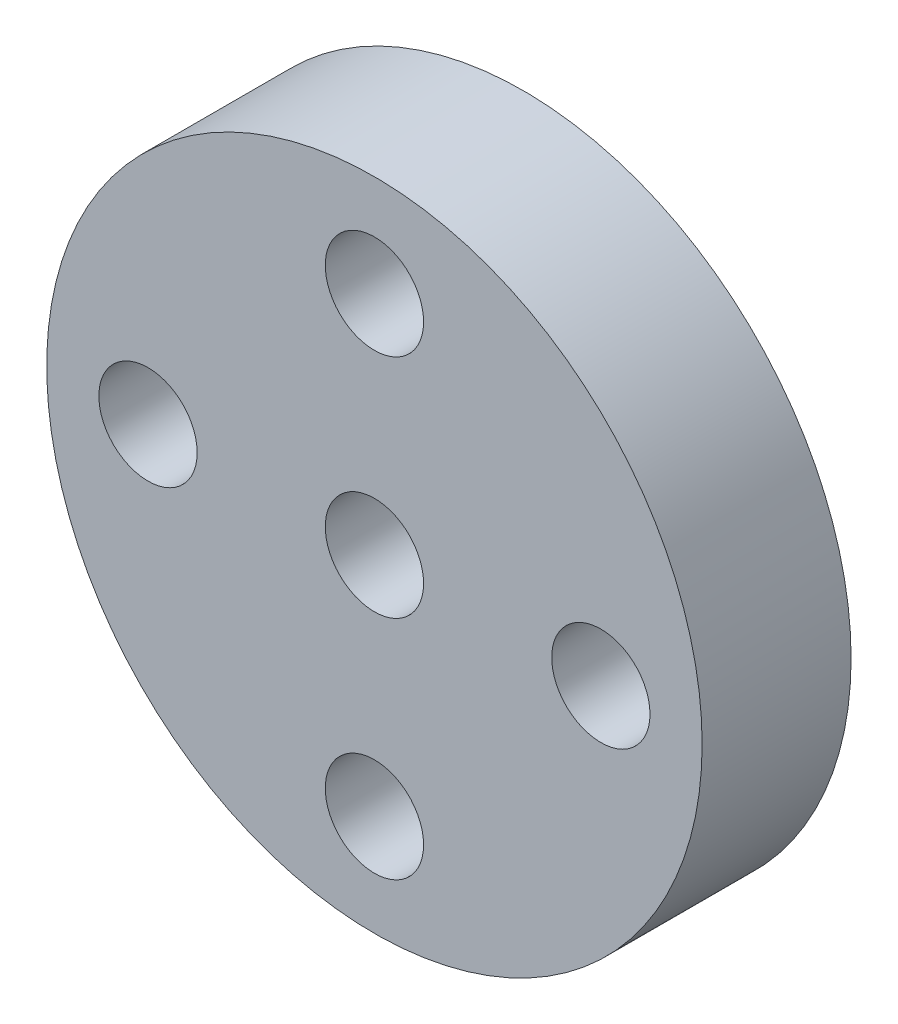
SolidWorks part; units mm, degrees
ref_plane "前视基准面" through (0, 0, 0) normal (0, 0, 1) x (1, 0, 0)
ref_plane "上视基准面" through (0, 0, 0) normal (0, 1, 0) x (1, 0, 0)
ref_plane "右视基准面" through (0, 0, 0) normal (1, 0, 0) x (0, 0, -1)
other "Configuration Table"
sketch "Sketch1" plane through (0, 0, 0) normal (0, 0, 1) x (1, 0, 0)
  circle A1 centre (-8.4373, 0.2507) radius 11
  dimension "D1" = 22
  dimension "D2" = 8.4373
  dimension "D6" = 0.2507
extrude "Boss-Extrude1" add sketch "Sketch1" along normal blind 5
sketch "Sketch2" plane through (0, 0, 5) normal (0, 0, 1) x (1, 0, 0)
  circle A0 centre (-8.4373, 0.2507) radius 11 construction
  circle A1 centre (-8.4373, 0.2507) radius 11
  circle A2 centre (-8.4373, 7.8507) radius 1.65
  circle A3 centre (-0.8373, 0.2507) radius 1.65
  circle A4 centre (-8.4373, -7.3493) radius 1.65
  circle A5 centre (-16.0373, 0.2507) radius 1.65
  circle A6 centre (-8.4373, 0.2507) radius 1.65
  point P15 (-8.4373, 0.2507)
  dimension "D1" = 3.3
  dimension "D4" = 3.3
  dimension "D2" = 7.6
  dimension "D3" = 4
extrude "Cut-Extrude2" cut sketch "Sketch2" against normal blind 21 contours A3 | A6 | A2 | A5 | A4
